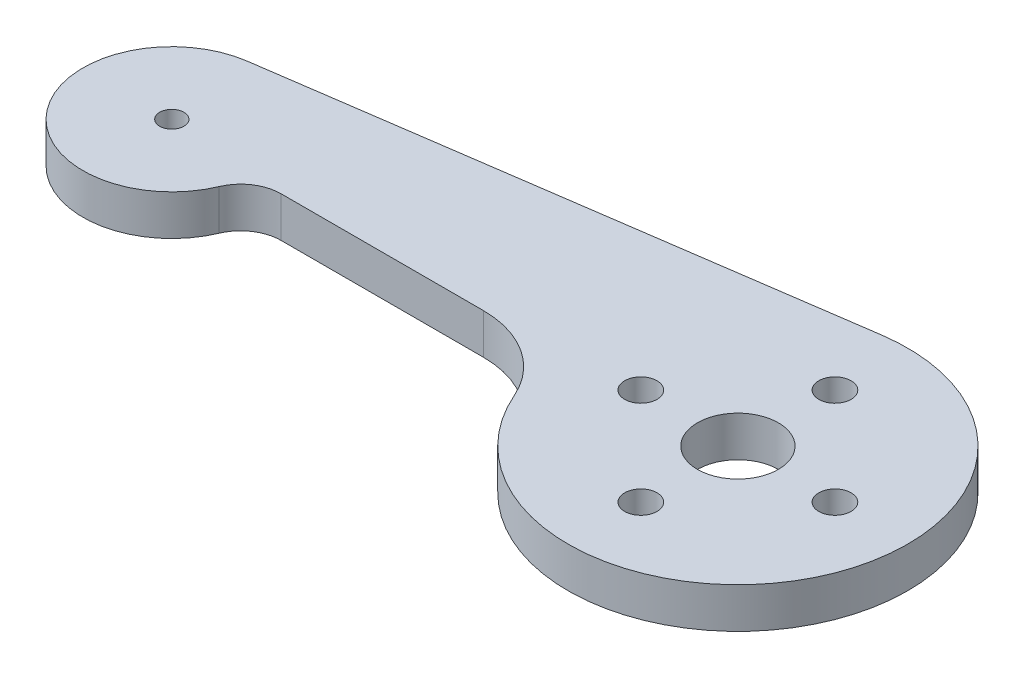
SolidWorks part; units mm, degrees
ref_plane "Front Plane" through (0, 0, 0) normal (0, 0, 1) x (1, 0, 0)
ref_plane "Top Plane" through (0, 0, 0) normal (0, 1, 0) x (1, 0, 0)
ref_plane "Right Plane" through (0, 0, 0) normal (1, 0, 0) x (0, 0, -1)
sketch "Sketch1" plane through (0, 0, 0) normal (0, 1, 0) x (1, 0, 0)
  line L0 (0, 0) -> (70, 0) construction
  line L1 (70, 0) -> (82, 0) construction
  line L2 (70, 0) -> (70, 12) construction
  line L3 (-1.5714, 10.8872) -> (67, 20.7846)
  line L4 (58, 0) -> (50.7588, -8.4127) construction
  line L5 (14.7415, -1.22) -> (39.7638, -1.22)
  circle A0 centre (0, 0) radius 1.5
  arc A1 (-1.5714, 10.8872) -> (10.1348, -4.2763) centre (0, 0) ccw
  circle A2 centre (70, 0) radius 5
  circle A3 centre (70, 0) radius 12 construction
  arc A4 (50.7588, -8.4127) -> (67, 20.7846) centre (70, 0) ccw
  circle A5 centre (70, 12) radius 2
  circle A6 centre (82, 0) radius 2
  circle A7 centre (70, -12) radius 2
  circle A8 centre (58, 0) radius 2
  arc A9 (14.7415, -1.22) -> (10.1348, -4.2763) centre (14.7415, -6.22) ccw
  arc A10 (50.7588, -8.4127) -> (39.7638, -1.22) centre (39.7638, -13.22) ccw
  point P17 (0, 0)
  point P21 (12.4184, -18.185)
  point P24 (14.4501, -6.8699)
  dimension "D1" = 3
  dimension "D2" = 22
  dimension "D4" = 10
  dimension "D5" = 24
  dimension "D6" = 42
  dimension "D7" = 4
  dimension "D9" = 4
  dimension "D10" = 4
  dimension "D11" = 4
  dimension "D12" = 10
  dimension "D13" = 24
  dimension "D3" = 70
  dimension "D8" = 90
  dimension "D14" = 11.1
extrude "Boss-Extrude1" add sketch "Sketch1" along normal blind 5
